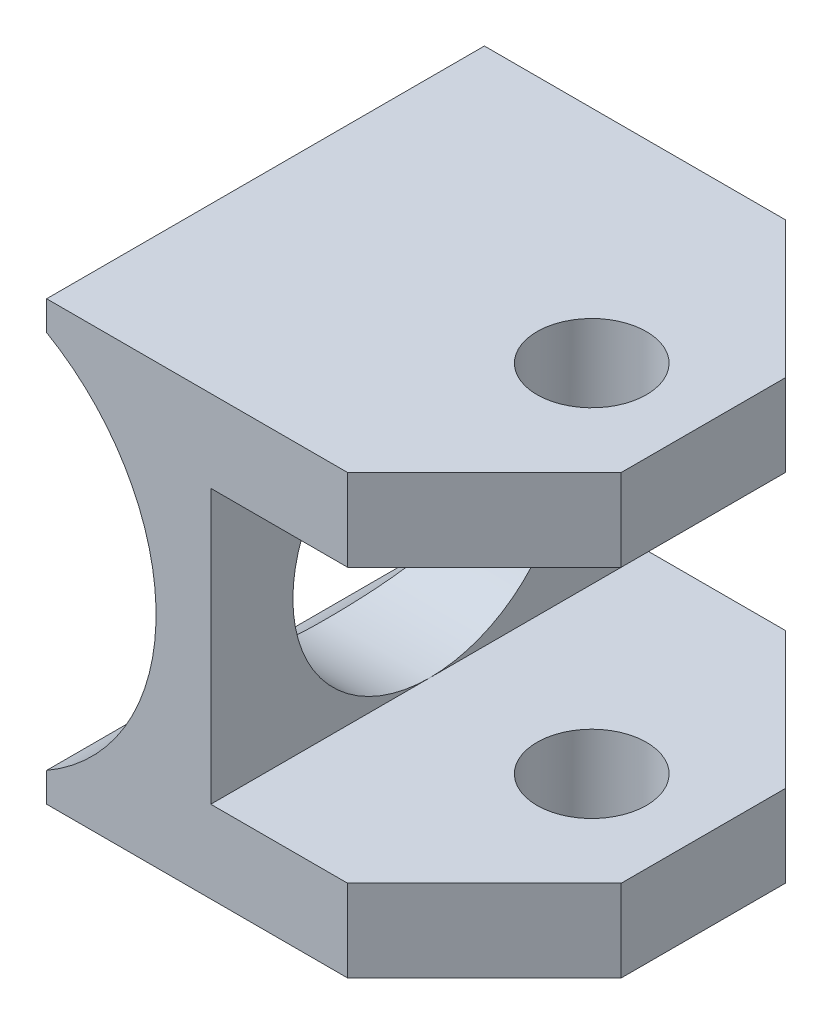
SolidWorks part; units mm, degrees
ref_plane "Front" through (0, 0, 0) normal (0, 0, 1) x (1, 0, 0)
ref_plane "Top" through (0, 0, 0) normal (0, 1, 0) x (1, 0, 0)
ref_plane "Right" through (0, 0, 0) normal (1, 0, 0) x (0, 0, -1)
sketch "Sketch1" plane through (0, 0, 0) normal (0, 0, 1) x (1, 0, 0)
  line L0 (6.35, 12.7) -> (31.75, 12.7)
  line L1 (31.75, 12.7) -> (31.75, 7.9375)
  line L2 (31.75, 7.9375) -> (15.875, 7.9375)
  line L3 (15.875, 7.9375) -> (15.875, -7.9375)
  line L4 (0, 0) -> (31.75, 0) construction
  line L5 (25.4, 12.7) -> (25.4, 0) construction
  line L6 (6.35, 12.7) -> (6.35, 10.9985)
  line L7 (31.75, -7.9375) -> (15.875, -7.9375)
  line L8 (31.75, -12.7) -> (31.75, -7.9375)
  line L9 (6.35, -12.7) -> (31.75, -12.7)
  line L10 (6.35, -12.7) -> (6.35, -10.9985)
  arc A0 (6.35, -10.9985) -> (6.35, 10.9985) centre (0, 0) ccw
  point P5 (12.7, 0)
  point P12 (15.875, 0)
  dimension "D1" = 25.4
  dimension "D2" = 7.9375
  dimension "D3" = 25.4
  dimension "D4" = 3.175
  dimension "D5" = 6.35
  dimension "D6" = 6.35
extrude "Boss-Extrude1" add sketch "Sketch1" along normal blind 25.4
hole_wizard "1/4 (0.25) Diameter Hole1" positions "Sketch2" profile "Sketch4" hole size "1/4" standard "ANSI Inch" end condition through all
sketch "Sketch2" plane through (0, 12.7, 0) normal (0, 1, 0) x (1, 0, 0)
  point P0 (25.4, -12.8218)
sketch "Sketch4" plane through (25.4, 12.7, 12.8218) normal (1, 0, 0) x (0, 0, 1)
  line L0 (0, 0) -> (0, 25.4)
  line L1 (0, 25.4) -> (3.175, 25.4)
  line L2 (3.175, 25.4) -> (3.175, 0)
  line L5 (3.175, 0) -> (0, 0)
  line L11 (0, -6.35) -> (0, 107.95) construction
  dimension "Thru Hole Dia." = 6.35
  dimension "Thru Hole Depth" = 25.4
chamfer "Chamfer1" distance 7.9375 angle 45 4 edges at (31.75, 10.3188, 0) (31.75, -10.3188, 0) (31.75, -10.3188, 25.4) (31.75, 10.3188, 25.4)
sketch3d "3DSketch1"
  line L0 (25.4, 12.7, 12.8218) -> (25.4, -12.7, 12.8218)
  circle A0 centre (25.4, 12.7, 12.8218) radius 3.175 construction
  circle A1 centre (25.4, -12.7, 12.8218) radius 3.175 construction
  point P3 (25.4, 0, 12.8218)
  point P6 (25.4, 15.875, 12.8218)
  point P9 (25.4, -9.525, 12.8218)
sketch "Sketch6" plane through (15.875, 0, 0) normal (1, 0, 0) x (0, 0, -1)
  line L0 (-25.4, 0) -> (0, 0) construction
  line L1 (-25.4, -7.9375) -> (-25.4, 7.9375) construction
  circle A0 centre (-12.7, 0) radius 7.9375
  dimension "D1" = 15.875
extrude "Cut-Extrude1" cut sketch "Sketch6" against normal through all
equation "\"D2@Sketch1\"=(.375)/2+.125"
